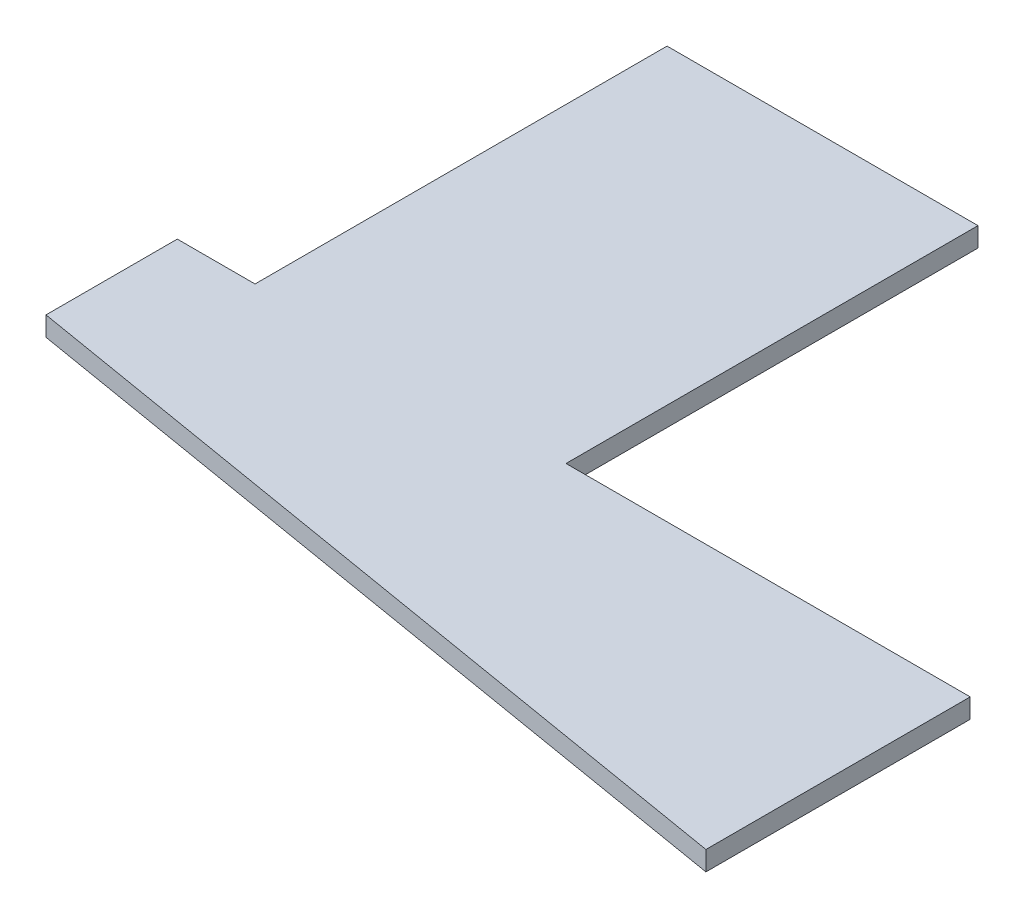
SolidWorks part; units mm, degrees
material "Plywood"
ref_plane "Front Plane" through (0, 0, 0) normal (0, 0, 1) x (1, 0, 0)
ref_plane "Top Plane" through (0, 0, 0) normal (0, 1, 0) x (1, 0, 0)
ref_plane "Right Plane" through (0, 0, 0) normal (1, 0, 0) x (0, 0, -1)
sketch "Sketch2" plane through (0, 0, 0) normal (0, 1, 0) x (1, 0, 0)
  line L0 (50.8, 0) -> (116.84, 0)
  line L2 (0, 0) -> (0, 67.31)
  line L3 (0, 67.31) -> (50.8, 67.31)
  line L4 (50.8, 0) -> (50.8, 67.31)
  line L5 (-55, 0) -> (55, 0) construction
  line L7 (116.84, -43.18) -> (-12.7, -21.4492)
  line L8 (-12.7, -21.4492) -> (-12.7, 0)
  line L9 (-12.7, 0) -> (0, 0)
  line L11 (116.84, -43.18) -> (116.84, 0)
  dimension "D1" = 50.8
  dimension "D2" = 67.31
  dimension "D3" = 66.04
  dimension "D4" = 12.7
  dimension "D5" = 43.18
extrude "Boss-Extrude1" add sketch "Sketch2" along normal blind 3.175
